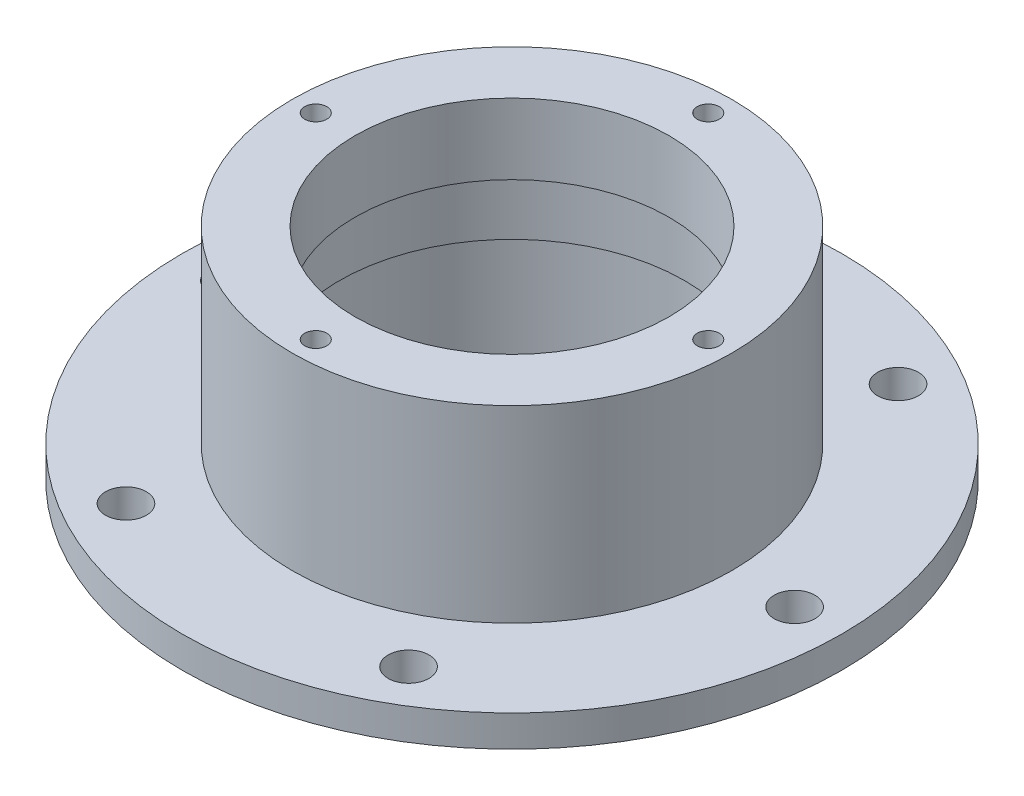
SolidWorks part; units mm, degrees
ref_plane "Front Plane" through (0, 0, 0) normal (0, 0, 1) x (1, 0, 0)
ref_plane "Top Plane" through (0, 0, 0) normal (0, 1, 0) x (1, 0, 0)
ref_plane "Right Plane" through (0, 0, 0) normal (1, 0, 0) x (0, 0, -1)
sketch "Sketch1" plane through (0, 0, 0) normal (0, 1, 0) x (1, 0, 0)
  circle A0 centre (0, 0) radius 105
  dimension "D1" = 210
extrude "Boss-Extrude1" add sketch "Sketch1" along normal blind 75
sketch "Sketch3" plane through (0, 0, 0) normal (0, -1, 0) x (1, 0, 0)
  circle A0 centre (0, 0) radius 105 construction
  circle A1 centre (0, 0) radius 105
  circle A2 centre (0, 0) radius 65
  dimension "D1" = 130
extrude "Cut-Extrude1" cut sketch "Sketch3" against normal blind 5
sketch "Sketch4" plane through (0, 0, 0) normal (0, -1, 0) x (1, 0, 0)
  circle A0 centre (0, 0) radius 105 construction
  circle A1 centre (0, 0) radius 105
  circle A2 centre (0, 0) radius 70
  dimension "D1" = 140
extrude "Cut-Extrude2" cut sketch "Sketch4" against normal up to next from offset 15 offset against normal yes
sketch "Sketch5" plane through (0, 0, 0) normal (0, -1, 0) x (1, 0, 0)
  circle A0 centre (0, 0) radius 55.4
  dimension "D1" = 110.8
extrude "Cut-Extrude3" cut sketch "Sketch5" against normal blind 32.5
sketch "Sketch6" plane through (0, 32.5, 0) normal (0, -1, 0) x (1, 0, 0)
  circle A0 centre (0, 0) radius 55
  dimension "D1" = 110
extrude "Cut-Extrude4" cut sketch "Sketch6" against normal blind 20
sketch "Sketch7" plane through (0, 52.5, 0) normal (0, -1, 0) x (1, 0, 0)
  circle A0 centre (0, 0) radius 50
  dimension "D1" = 100
extrude "Cut-Extrude5" cut sketch "Sketch7" against normal up to next
hole_wizard "Ø12.0mm Dowel Hole1" positions "Sketch9" profile "Sketch10" hole size "Ø12.0" standard "ISO" end condition through all
sketch "Sketch9" plane through (0, 15, 0) normal (0, 1, 0) x (1, 0, 0)
  circle A0 centre (0, 0) radius 90 construction
  point P8 (90, 0)
  point P15 (45, -77.9423)
  point P16 (-45, -77.9423)
  point P17 (-90, 0)
  point P18 (-45, 77.9423)
  point P19 (45, 77.9423)
  dimension "D1" = 180
  dimension "D2" = 6
sketch "Sketch10" plane through (45, 15, -77.9423) normal (1, 0, 0) x (0, 0, 1)
  line L0 (0, 0) -> (0, 15)
  line L1 (0, 15) -> (6.5, 15)
  line L2 (6.5, 15) -> (6.5, 0)
  line L5 (6.5, 0) -> (0, 0)
  line L11 (0, -6.35) -> (0, 107.95) construction
  dimension "Thru Hole Dia." = 13
  dimension "Thru Hole Depth" = 15
hole_wizard "Ø6.0mm Dowel Hole1" positions "Sketch12" profile "Sketch13" hole size "Ø6.0" standard "ISO" end condition through all
sketch "Sketch12" plane through (0, 75, 0) normal (0, 1, 0) x (1, 0, 0)
  circle A0 centre (0, 0) radius 62.5 construction
  point P7 (0, 62.5)
  point P9 (62.5, 0)
  point P11 (0, -62.5)
  point P15 (-62.5, 0)
  dimension "D1" = 125
sketch "Sketch13" plane through (-62.5, 75, 0) normal (1, 0, 0) x (0, 0, 1)
  line L0 (0, 0) -> (0, 75)
  line L1 (0, 75) -> (3.5, 75)
  line L2 (3.5, 75) -> (3.5, 0)
  line L5 (3.5, 0) -> (0, 0)
  line L11 (0, -6.35) -> (0, 107.95) construction
  dimension "Thru Hole Dia." = 7
  dimension "Thru Hole Depth" = 75
